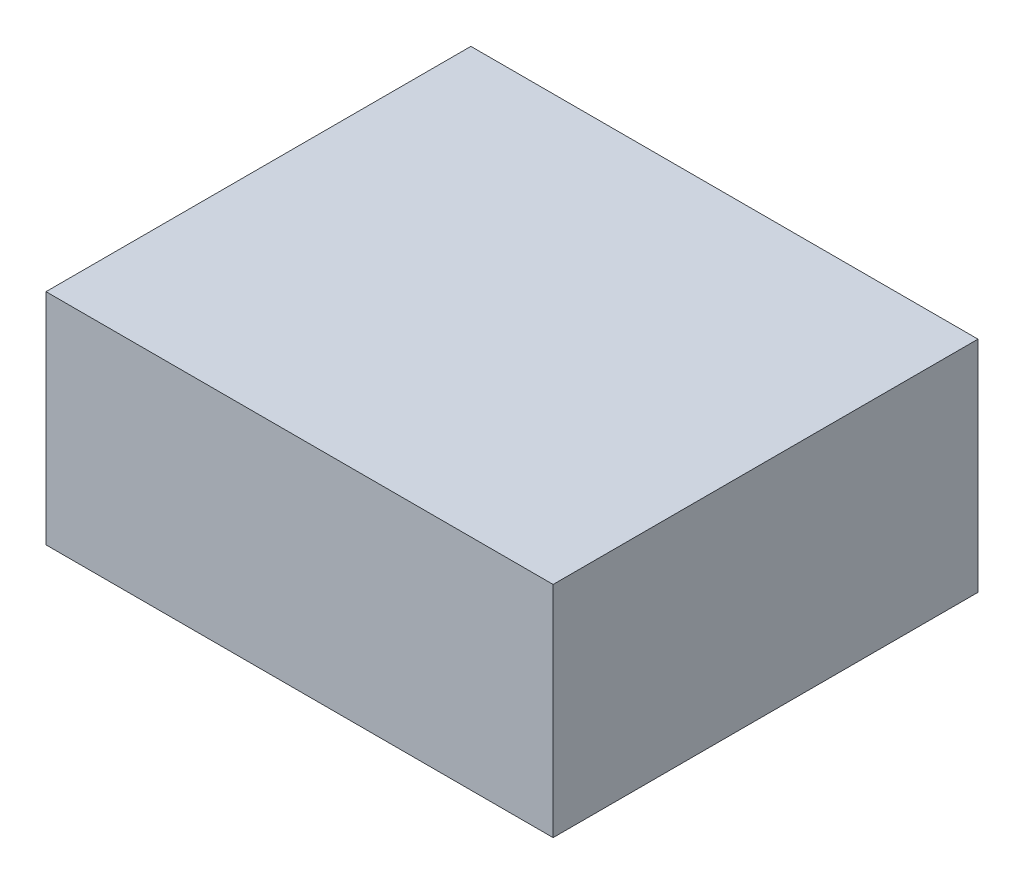
SolidWorks part; units mm, degrees
ref_plane "Front Plane" through (0, 0, 0) normal (0, 0, 1) x (1, 0, 0)
ref_plane "Top Plane" through (0, 0, 0) normal (0, 1, 0) x (1, 0, 0)
ref_plane "Right Plane" through (0, 0, 0) normal (1, 0, 0) x (0, 0, -1)
sketch "USBPort Sketch" plane through (0, 0, 0) normal (0, 1, 0) x (1, 0, 0)
  line L1 (0, 0) -> (9.25, 0)
  line L2 (0, 0) -> (0, 7.75)
  line L3 (0, 7.75) -> (9.25, 7.75)
  line L4 (9.25, 0) -> (9.25, 7.75)
  dimension "USBThing Width" = 9.25
  dimension "USBThing Length" = 7.75
extrude "USBPort Extrude" add sketch "USBPort Sketch" along normal blind 4
